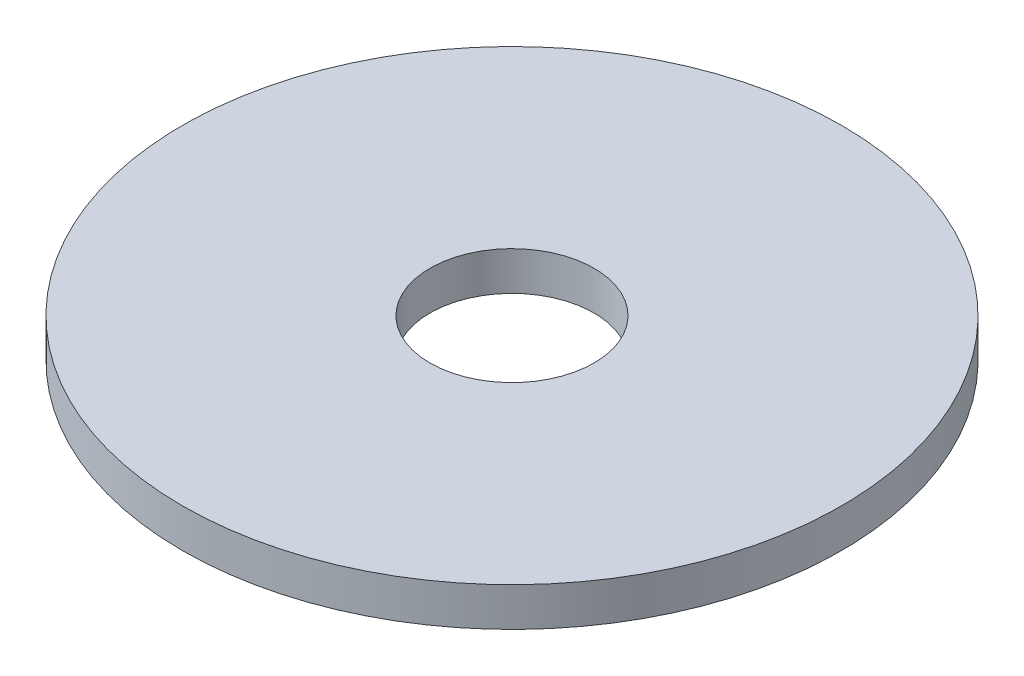
SolidWorks part; units mm, degrees
ref_plane "Front Plane" through (0, 0, 0) normal (0, 0, 1) x (1, 0, 0)
ref_plane "Top Plane" through (0, 0, 0) normal (0, 1, 0) x (1, 0, 0)
ref_plane "Right Plane" through (0, 0, 0) normal (1, 0, 0) x (0, 0, -1)
sketch "Sketch1" plane through (0, 0, 0) normal (0, 1, 0) x (1, 0, 0)
  circle A0 centre (0, 0) radius 3.175
  circle A1 centre (0, 0) radius 12.75
  dimension "D1" = 6.35
  dimension "D2" = 25.5
extrude "Boss-Extrude1" add sketch "Sketch1" along normal blind 1.5
